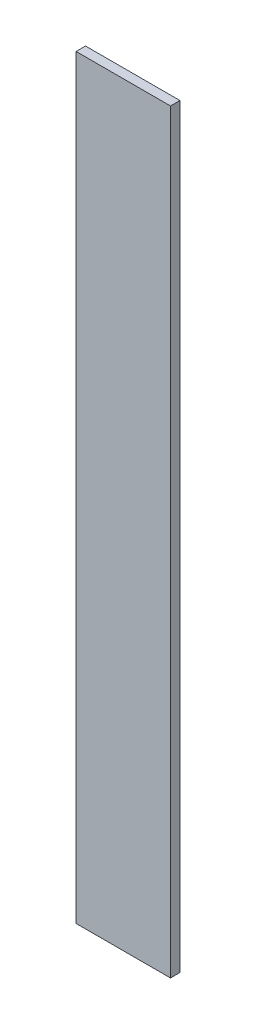
SolidWorks part; units mm, degrees
ref_plane "Front Plane" through (0, 0, 0) normal (0, 0, 1) x (1, 0, 0)
ref_plane "Top Plane" through (0, 0, 0) normal (0, 1, 0) x (1, 0, 0)
ref_plane "Right Plane" through (0, 0, 0) normal (1, 0, 0) x (0, 0, -1)
sketch "Sketch1" plane through (0, 0, 0) normal (0, 0, 1) x (1, 0, 0)
  line L1 (-12.7, -101.6) -> (12.7, -101.6)
  line L2 (-12.7, -101.6) -> (-12.7, 101.6)
  line L3 (-12.7, 101.6) -> (12.7, 101.6)
  line L4 (12.7, -101.6) -> (12.7, 101.6)
  line L5 (-12.7, -101.6) -> (12.7, 101.6) construction
  line L6 (-12.7, 101.6) -> (12.7, -101.6) construction
  point P0 (0, 0)
  dimension "D1" = 25.4
  dimension "D2" = 203.2
extrude "Boss-Extrude1" add sketch "Sketch1" along normal blind 2.54
